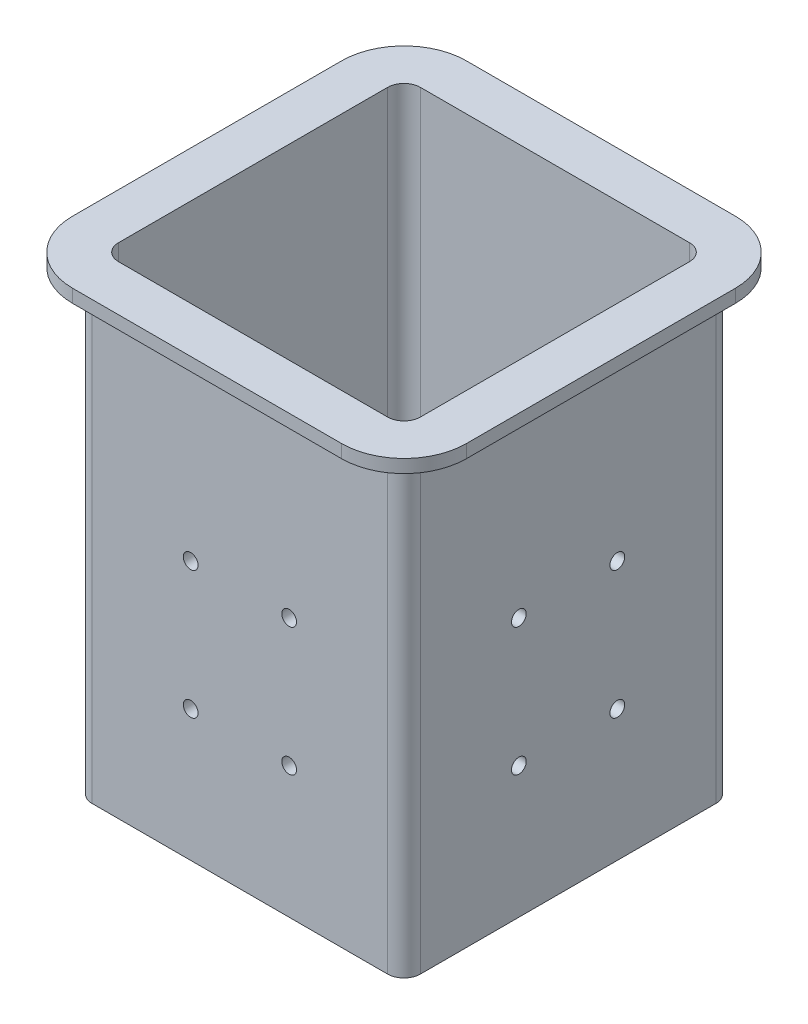
SolidWorks part; units mm, degrees
ref_plane "Front Plane" through (0, 0, 0) normal (0, 0, 1) x (1, 0, 0)
ref_plane "Top Plane" through (0, 0, 0) normal (0, 1, 0) x (1, 0, 0)
ref_plane "Right Plane" through (0, 0, 0) normal (1, 0, 0) x (0, 0, -1)
sketch "Sketch1" plane through (0, 0, 0) normal (0, 1, 0) x (1, 0, 0)
  line L0 (50, -50) -> (-50, 50) construction
  line L1 (-50, 50) -> (50, 50)
  line L2 (-50, 50) -> (-50, -50)
  line L3 (-50, -50) -> (50, -50)
  line L4 (50, 50) -> (50, -50)
  line L5 (-50, -50) -> (50, 50) construction
  line L6 (0, 33.45) -> (0, -33.45) construction
  line L7 (33.45, 33.45) -> (-33.45, 33.45) construction
  line L8 (33.45, 33.45) -> (33.45, -33.45) construction
  line L9 (33.45, -33.45) -> (-33.45, -33.45) construction
  line L10 (-33.45, 33.45) -> (-33.45, -33.45) construction
  circle A0 centre (0, 0) radius 10
  circle A1 centre (33.45, 33.45) radius 2.75
  circle A2 centre (33.45, -33.45) radius 2.75
  circle A3 centre (-33.45, -33.45) radius 2.75
  circle A4 centre (-33.45, 33.45) radius 2.75
  point P7 (0, 0)
  dimension "D1" = 20
  dimension "D4" = 5.5
  dimension "D2" = 100
  dimension "D3" = 66.9
extrude "Boss-Extrude1" add sketch "Sketch1" along normal blind 4
sketch "Sketch2" plane through (0, 4, 0) normal (0, 1, 0) x (1, 0, 0)
  line L0 (-46, 46) -> (-50, 46) construction
  line L1 (-50, -50) -> (50, -50)
  line L2 (-50, -50) -> (-50, 50)
  line L3 (-50, 50) -> (50, 50)
  line L4 (50, -50) -> (50, 50)
  line L5 (-46, -46) -> (46, -46)
  line L6 (-46, -46) -> (-46, 46)
  line L7 (-46, 46) -> (46, 46)
  line L8 (46, -46) -> (46, 46)
  line L9 (-46, 46) -> (-46, 50) construction
  line L10 (46, -46) -> (46, -50) construction
  line L11 (46, -50) -> (46, -46) construction
  line L12 (46, -46) -> (50, -46) construction
  dimension "D1" = 4
extrude "Boss-Extrude2" add sketch "Sketch2" along normal blind 135
fillet "Fillet1" radius 5 8 edges at (-50, 69.5, 50) (50, 69.5, 50) (50, 69.5, -50) (-50, 69.5, -50) (46, 71.5, 46) (-46, 71.5, 46) (-46, 71.5, -46) (46, 71.5, -46)
sketch "Sketch3" plane through (0, 139, 0) normal (0, 1, 0) x (1, 0, 0)
  line L0 (-41, 46) -> (41, 46)
  line L1 (46, 41) -> (46, -41)
  line L2 (41, -46) -> (-41, -46)
  line L3 (-46, -41) -> (-46, 41)
  line L4 (46, -41) -> (46, 41) construction
  line L5 (-41, -46) -> (41, -46) construction
  line L6 (-46, 41) -> (-46, -41) construction
  line L7 (-41, 60) -> (41, 60)
  line L8 (60, 41) -> (60, -41)
  line L9 (41, -60) -> (-41, -60)
  line L10 (-60, -41) -> (-60, 41)
  arc A0 (-41, 46) -> (-46, 41) centre (-41, 41) ccw
  arc A1 (-41, -46) -> (-46, -41) centre (-41, -41) cw
  arc A2 (46, -41) -> (41, -46) centre (41, -41) cw
  arc A3 (41, 46) -> (46, 41) centre (41, 41) cw
  arc A4 (41, 60) -> (60, 41) centre (41, 41) cw
  arc A5 (60, -41) -> (41, -60) centre (41, -41) cw
  arc A6 (-41, -60) -> (-60, -41) centre (-41, -41) cw
  arc A7 (-41, 60) -> (-60, 41) centre (-41, 41) ccw
  dimension "D1" = 5
  dimension "D2" = 14
extrude "Boss-Extrude3" add sketch "Sketch3" along normal blind 4
fillet "Fillet2" radius 2 8 edges at (0, 139, -50) (48.5355, 139, -48.5355) (50, 139, 0) (48.5355, 139, 48.5355) (0, 139, 50) (-48.5355, 139, 48.5355) (-50, 139, 0) (-48.5355, 139, -48.5355)
sketch "Sketch4" plane through (50, 0, 0) normal (1, 0, 0) x (0, 0, -1)
  line L0 (-15, 40) -> (-50, 40) construction
  line L1 (-50, 0) -> (-50, 137) construction
  line L2 (15, 40) -> (50, 40) construction
  line L3 (50, 137) -> (50, 0) construction
  line L4 (-15, 40) -> (0, 0) construction
  line L5 (0, 0) -> (15, 40) construction
  circle A0 centre (-15, 79) radius 2.25
  circle A1 centre (15, 79) radius 2.25
  circle A2 centre (15, 40) radius 2.25
  circle A3 centre (-15, 40) radius 2.25
  dimension "D1" = 4.5
  dimension "D2" = 39
  dimension "D3" = 30
  dimension "D4" = 40
extrude "Cut-Extrude1" cut sketch "Sketch4" against normal up to next
sketch "Sketch5" plane through (0, 0, 50) normal (0, 0, 1) x (1, 0, 0)
  line L0 (-15, 40) -> (0, 0) construction
  line L1 (0, 0) -> (15, 40) construction
  line L2 (-45, 0) -> (45, 0) construction
  circle A0 centre (15, 79) radius 2.25
  circle A1 centre (-15, 79) radius 2.25
  circle A2 centre (-15, 40) radius 2.25
  circle A3 centre (15, 40) radius 2.25
  dimension "D1" = 4.5
  dimension "D2" = 40
  dimension "D3" = 30
  dimension "D4" = 39
extrude "Cut-Extrude2" cut sketch "Sketch5" against normal up to next
